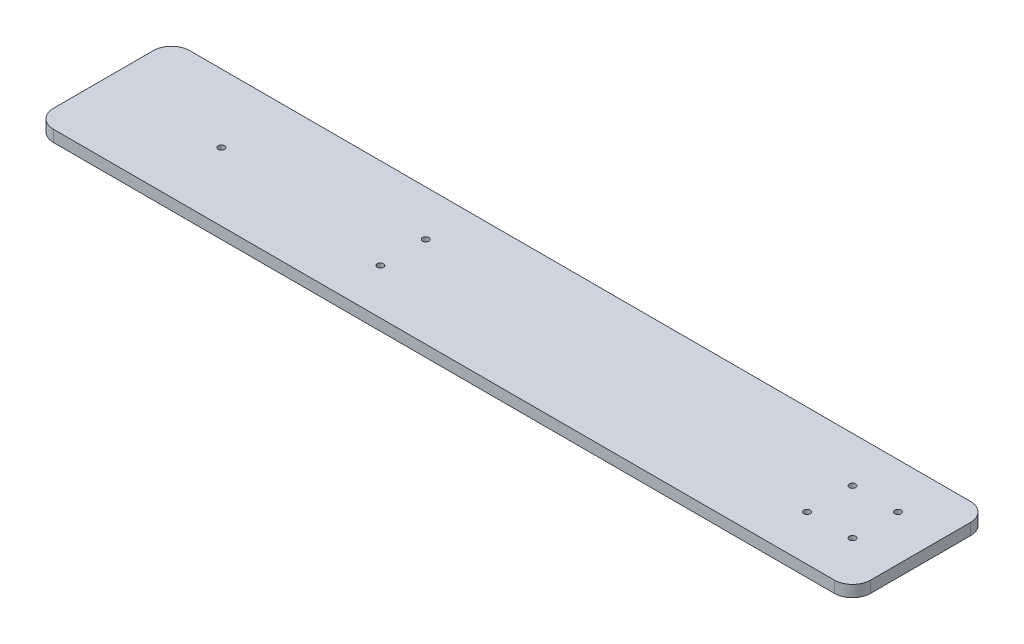
SolidWorks part; units mm, degrees
ref_plane "Front Plane" through (0, 0, 0) normal (0, 0, 1) x (1, 0, 0)
ref_plane "Top Plane" through (0, 0, 0) normal (0, 1, 0) x (1, 0, 0)
ref_plane "Right Plane" through (0, 0, 0) normal (1, 0, 0) x (0, 0, -1)
sketch "Sketch12" plane through (0, 0, 0) normal (0, 1, 0) x (1, 0, 0)
  line L1 (-225, 37.5) -> (225, 37.5)
  line L2 (-225, 37.5) -> (-225, -37.5)
  line L3 (-225, -37.5) -> (225, -37.5)
  line L4 (225, 37.5) -> (225, -37.5)
  line L5 (-225, 37.5) -> (225, -37.5) construction
  line L6 (-225, -37.5) -> (225, 37.5) construction
  point P0 (0, 0)
  dimension "D1" = 450
  dimension "D2" = 75
extrude "Boss-Extrude2" add sketch "Sketch12" along normal blind 6.35
sketch "Sketch13" plane through (0, 0, 0) normal (0, -1, 0) x (1, 0, 0)
  line L0 (225, -37.5) -> (-225, -37.5) construction
  line L2 (225, 37.5) -> (225, -37.5) construction
  circle A0 centre (175, -12.5) radius 1.75
  point P4 (225, 0)
  dimension "D1" = 25
  dimension "D3" = 3.5
  dimension "D2" = 50
extrude "Cut-Extrude1" cut sketch "Sketch13" against normal through all
pattern_linear "LPattern1" count 2 spacing 25 along (1, 0, 0) of "Cut-Extrude1"
pattern_linear "LPattern2" count 2 spacing 25 along (0, 0, 1) of "LPattern1", "Cut-Extrude1"
sketch "Sketch15" plane through (0, 0, 0) normal (0, -1, 0) x (1, 0, 0)
  line L0 (225, 37.5) -> (225, -37.5) construction
  line L1 (-225, 37.5) -> (225, 37.5) construction
  circle A0 centre (-160, 0) radius 1.75
  dimension "D1" = 385
  dimension "D2" = 3.5
  dimension "D3" = 37.5
extrude "Cut-Extrude2" cut sketch "Sketch15" against normal through all
fillet "Fillet1" radius 10 4 edges at (225, 3.175, -37.5) (225, 3.175, 37.5) (-225, 3.175, 37.5) (-225, 3.175, -37.5)
sketch "Sketch17" plane through (0, 6.35, 0) normal (0, 1, 0) x (1, 0, 0)
  line L0 (-215, -37.5) -> (215, -37.5) construction
  line L1 (215, 37.5) -> (-215, 37.5) construction
  circle A0 centre (-60, 12.5) radius 1.75
  circle A1 centre (-60, -12.5) radius 1.75
  dimension "D1" = 3.5
  dimension "D2" = 3.5
  dimension "D3" = 100
  dimension "D4" = 100
  dimension "D5" = 25
  dimension "D6" = 25
extrude "Cut-Extrude3" cut sketch "Sketch17" against normal through all
